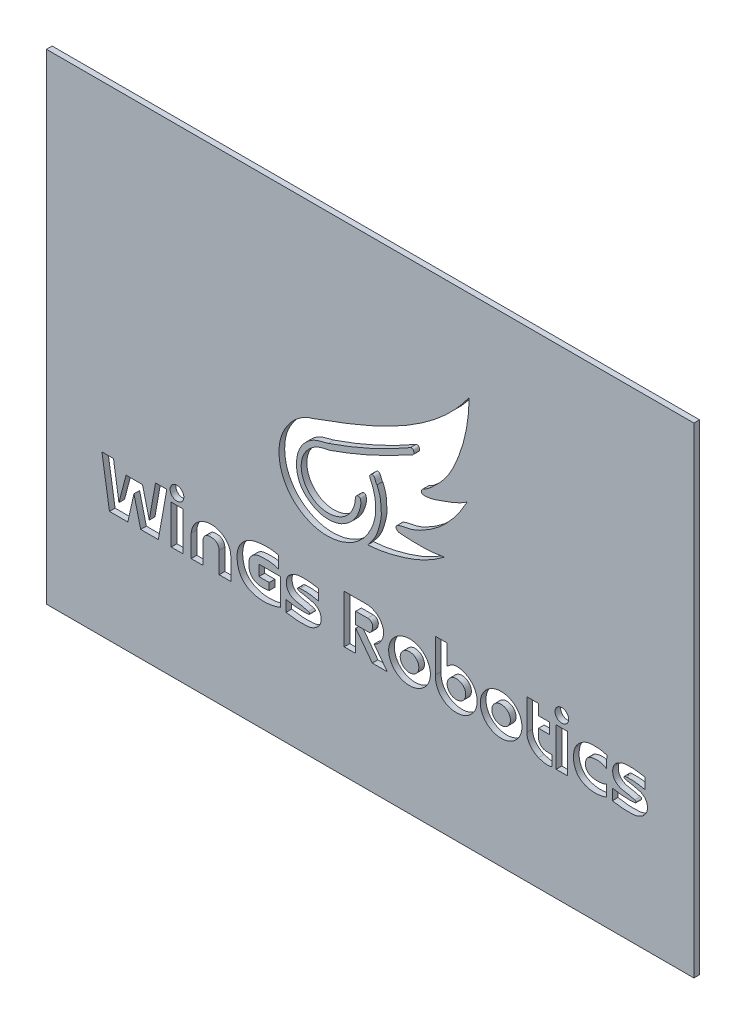
SolidWorks part; units mm, degrees
ref_plane "前视基准面" through (0, 0, 0) normal (0, 0, 1) x (1, 0, 0)
ref_plane "上视基准面" through (0, 0, 0) normal (0, 1, 0) x (1, 0, 0)
ref_plane "右视基准面" through (0, 0, 0) normal (1, 0, 0) x (0, 0, -1)
other "Configuration Table"
sketch "Sketch1" plane through (0, 0, 0) normal (0, 0, 1) x (1, 0, 0)
  line L1 (0, 0) -> (114.5, 0)
  line L2 (0, 0) -> (0, 85)
  line L3 (0, 85) -> (114.5, 85)
  line L4 (114.5, 0) -> (114.5, 85)
  dimension "D1" = 114.5
  dimension "D2" = 85
extrude "Boss-Extrude1" add sketch "Sketch1" along normal blind 1
sketch "Sketch2" plane through (0, 0, 1) normal (0, 0, 1) x (1, 0, 0)
  line L0 (9.8027, 28.235) -> (11.8527, 28.235)
  line L1 (11.8527, 28.235) -> (12.8123, 21.9684)
  line L2 (12.8123, 21.9684) -> (14.0773, 26.8101)
  line L3 (14.0773, 26.8101) -> (16.9852, 26.8101)
  line L4 (16.9852, 26.8101) -> (18.1775, 21.9684)
  line L5 (18.1775, 21.9684) -> (19.2825, 28.235)
  line L6 (19.2825, 28.235) -> (21.2744, 28.235)
  line L7 (21.2744, 28.235) -> (19.7853, 19.7903)
  line L8 (19.7853, 19.7903) -> (16.6653, 19.7903)
  line L9 (16.6653, 19.7903) -> (15.4678, 24.6536)
  line L10 (15.4678, 24.6536) -> (14.3826, 19.7903)
  line L11 (14.3826, 19.7903) -> (11.1403, 19.7903)
  line L12 (11.1403, 19.7903) -> (9.8027, 28.235)
  line L13 (22.0595, 26.6647) -> (24.1096, 26.6647)
  line L14 (24.1096, 26.6647) -> (24.1096, 19.7903)
  line L15 (24.1096, 19.7903) -> (22.0595, 19.7903)
  line L16 (22.0595, 19.7903) -> (22.0595, 26.6647)
  line L17 (32.5933, 23.6986) -> (32.5933, 19.7903)
  line L18 (32.5933, 19.7903) -> (30.5505, 19.7903)
  line L19 (30.5505, 19.7903) -> (30.5505, 23.5343)
  line L20 (27.6427, 23.5343) -> (27.6427, 19.7903)
  line L21 (27.6427, 19.7903) -> (25.5972, 19.7903)
  line L22 (25.5972, 19.7903) -> (25.5972, 23.6986)
  line L23 (41.4245, 20.2317) -> (41.4245, 24.9256)
  line L24 (41.4245, 24.9256) -> (37.5759, 24.9256)
  line L25 (37.5759, 24.9256) -> (37.5759, 23.026)
  line L26 (37.5759, 23.026) -> (39.3929, 23.026)
  line L27 (39.3929, 23.026) -> (39.3929, 21.7872)
  line L28 (41.0585, 28.009) -> (41.0585, 25.9029)
  line L29 (42.3726, 19.9426) -> (42.3726, 21.9041)
  line L30 (48.1482, 26.4281) -> (48.1482, 24.5174)
  line L31 (57.9509, 22.8769) -> (60.2681, 19.7995)
  line L32 (60.2681, 19.7995) -> (57.6234, 19.7995)
  line L33 (57.6234, 19.7995) -> (54.6991, 23.6831)
  line L34 (54.6991, 23.6831) -> (54.6991, 19.7995)
  line L35 (54.6991, 19.7995) -> (52.65, 19.7995)
  line L36 (52.65, 19.7995) -> (52.65, 28.3165)
  line L37 (52.65, 28.3165) -> (56.9933, 28.3165)
  line L38 (56.8114, 26.2746) -> (54.6991, 26.2746)
  line L39 (54.6991, 26.2746) -> (54.6991, 24.2045)
  line L40 (54.6991, 24.2045) -> (56.8948, 24.2045)
  line L41 (68.7934, 29.486) -> (70.8757, 29.486)
  line L42 (70.8757, 29.486) -> (70.8757, 25.9572)
  line L43 (68.7934, 29.486) -> (68.8194, 23.6311)
  line L44 (84.9748, 28.3165) -> (87.0193, 28.3165)
  line L45 (87.0193, 28.3165) -> (87.0193, 26.4281)
  line L46 (87.0193, 26.4281) -> (88.9274, 26.4281)
  line L47 (88.9274, 26.4281) -> (88.9274, 24.5174)
  line L48 (88.9274, 24.5174) -> (87.0193, 24.5174)
  line L49 (87.0193, 24.5174) -> (87.0193, 22.8769)
  line L50 (84.9748, 28.3165) -> (84.9748, 22.8769)
  line L51 (89.3697, 19.7903) -> (89.3697, 21.6564)
  line L52 (90.1423, 26.5997) -> (92.1233, 26.5997)
  line L53 (92.1233, 26.5997) -> (92.1233, 19.7903)
  line L54 (92.1233, 19.7903) -> (90.1423, 19.7903)
  line L55 (90.1423, 19.7903) -> (90.1423, 26.5997)
  line L56 (100.0817, 19.9352) -> (100.0817, 21.8967)
  line L57 (105.8573, 26.4207) -> (105.8573, 24.51)
  circle A0 centre (23.0773, 28.5403) radius 1.2139
  circle A1 centre (91.149, 28.5403) radius 1.2042
  ellipse E0 centre (64.2087, 23.2238) end of major axis (62.5755, 23.026) minor radius 1.6135
  ellipse E1 centre (64.2087, 23.2238) end of major axis (60.5207, 23.2238) minor radius 3.5863
  ellipse E2 centre (72.5089, 23.2351) end of major axis (70.8757, 23.0374) minor radius 1.6135
  ellipse E3 centre (72.4814, 23.2061) end of major axis (68.7937, 23.2519) minor radius 3.5627 (68.8194, 23.6311) -> (72.4501, 26.7688) ccw
  ellipse E4 centre (80.4111, 23.2582) end of major axis (78.7779, 23.0604) minor radius 1.6135
  ellipse E5 centre (80.4111, 23.2582) end of major axis (76.723, 23.2582) minor radius 3.5863
  spline S0 degree 3 poles (47.1831, 52.0268) (57.216, 55.6604) (68.3491, 59.9142) (74.7524, 69.0372) knots 0 0 0 0 1 1 1 1
  spline S1 degree 3 poles (74.7524, 69.0372) (74.7365, 65.3659) (73.7278, 60.4257) (70.9663, 54.8142) (68.7581, 52.5438) (67.3008, 51.2594) (66.3857, 50.8892) (66.1919, 50.0322) (67.3405, 50.0519) (68.5807, 50.2825) (71.1429, 51.2424) (73.2135, 51.9772) (74.4343, 52.9034) knots 0 0 0 0 0.360634 0.500005 0.614902 0.674582 0.691796 0.711227 0.738156 0.775636 0.851126 1 1 1 1
  spline S2 degree 3 poles (74.4343, 52.9034) (73.5344, 51.2446) (71.9363, 48.8706) (69.1717, 46.2263) (66.8129, 44.6852) (64.459, 43.5637) (62.7709, 43.442) (61.8385, 43.0103) (61.7928, 42.333) (62.306, 42.118) (62.5755, 42.1345) knots 0 0 0 0 0.317486 0.47747 0.639062 0.792073 0.904921 0.928219 0.95201 1 1 1 1
  spline S3 degree 3 poles (62.5755, 42.1345) (63.3547, 42.0538) (64.7001, 41.9914) (66.7084, 41.981) (68.5463, 42.1026) (69.8092, 42.2942) (70.4107, 42.4227) knots 0 0 0 0 0.298501 0.513418 0.765548 1 1 1 1
  spline S4 degree 3 poles (70.4107, 42.4227) (69.0722, 41.3928) (66.6735, 39.9566) (63.1137, 38.6779) (60.0189, 37.8594) (57.9209, 37.5758) (56.8114, 37.504) knots 0 0 0 0 0.345509 0.567874 0.772357 1 1 1 1
  spline S5 degree 3 poles (56.8114, 37.504) (57.1501, 38.014) (57.9873, 38.9045) (58.6132, 40.423) (59.0127, 41.8409) (59.2903, 43.2209) (59.1608, 44.4082) (59.1125, 45.8858) (58.7734, 46.8278) (58.4542, 47.5164) knots 0 0 0 0 0.171911 0.337536 0.453261 0.586014 0.727877 0.785411 1 1 1 1
  spline S6 degree 3 poles (58.4542, 47.5164) (58.1552, 47.7663) (58.2426, 48.4056) (57.6344, 48.7258) (57.3395, 48.5611) (57.1481, 48.3317) (57.1918, 47.9689) (57.3731, 47.5948) (57.6463, 47.0478) (57.8358, 46.4382) (58.0549, 45.6679) (58.1832, 44.9046) (58.2458, 43.8518) (58.2148, 42.7406) (57.9317, 41.5832) (57.6308, 40.6253) (57.1596, 39.7594) (56.5162, 38.6016) (55.4247, 37.4363) (54.1168, 36.4637) (52.8944, 35.9233) (51.7724, 35.5143) (50.4508, 35.3174) (48.7837, 35.2372) (46.8987, 35.6969) (44.9241, 36.6174) (43.1617, 38.1067) (42.0038, 39.9015) (41.341, 41.702) (41.0315, 43.7959) (41.2416, 46.0312) (42.3532, 48.424) (44.0891, 50.6501) (46.0639, 51.7314) (47.1831, 52.0268) knots 0 0 0 0 0.025484 0.033383 0.040232 0.046589 0.052344 0.063459 0.074884 0.093534 0.10647 0.129018 0.145625 0.17776 0.203591 0.22594 0.245355 0.270053 0.315285 0.351906 0.379455 0.405318 0.432327 0.469429 0.51742 0.561659 0.615846 0.670887 0.704018 0.744828 0.813277 0.85164 0.92215 1 1 1 1
  spline S7 degree 3 poles (64.3499, 56.1614) (64.4693, 56.198) (64.7382, 56.2478) (64.9298, 55.9871) (65.0268, 55.728) (64.8911, 55.1487) (64.274, 55.0547) (64.0386, 54.8823) knots 0 0 0 0 0.180535 0.288784 0.393192 0.542414 1 1 1 1
  spline S8 degree 3 poles (64.0386, 54.8823) (59.572, 52.4062) (54.9001, 50.2948) (50.0745, 48.6121) knots 0 0 0 0 1 1 1 1
  spline S9 degree 2 poles (64.3499, 56.1614) (57.4385, 52.1577) (49.8143, 49.5487) knots 0 0 0 1 1 1
  spline S10 degree 3 poles (49.8143, 49.5487) (49.1643, 49.3784) (48.2124, 49.1961) (46.3723, 48.3773) (44.2192, 46.161) (43.9774, 42.6043) (45.2254, 40.0525) (46.5951, 38.9146) (48.299, 37.9908) (50.179, 37.8379) (52.0127, 38.232) (53.3955, 39.1002) (54.5017, 40.1892) (55.1879, 41.4828) (55.5621, 42.6798) (55.6315, 43.5768) (55.4539, 44.1289) (55.208, 44.1161) knots 0 0 0 0 0.074167 0.1054 0.220595 0.394008 0.454413 0.527731 0.585289 0.665338 0.728528 0.788515 0.842168 0.897128 0.948286 0.97672 1 1 1 1
  spline S11 degree 3 poles (55.208, 44.1161) (55.0226, 44.1791) (54.667, 43.959) (54.6094, 43.4642) (54.5978, 42.8636) (54.3423, 42.0093) (53.7764, 40.7342) (52.3297, 39.3376) (50.1524, 38.7214) (47.7052, 39.1332) (45.9303, 40.6216) (44.9775, 42.794) (45.0428, 45.5373) (47.1244, 48.0082) (49.206, 48.4687) (50.0745, 48.6121) knots 0 0 0 0 0.023493 0.044042 0.061062 0.101136 0.156797 0.23921 0.350066 0.433771 0.549578 0.629423 0.732521 0.886291 1 1 1 1
  spline S12 degree 3 poles (25.5972, 23.6986) (25.655, 24.3658) (26.0941, 25.5117) (27.5424, 26.5737) (30.2768, 27.2067) (32.5736, 25.5619) (32.5933, 23.6986) knots 0 0 0 0 0.198571 0.34064 0.5135 1 1 1 1
  spline S13 degree 3 poles (30.5505, 23.5343) (30.5434, 23.9759) (30.1068, 24.7165) (29.076, 24.8585) (28.0074, 24.7723) (27.6729, 23.9331) (27.6427, 23.5343) knots 0 0 0 0 0.311205 0.495488 0.702071 1 1 1 1
  spline S14 degree 3 poles (41.0585, 28.009) (40.0534, 28.3395) (38.2528, 28.3483) (35.58, 27.8618) (33.8071, 26.0118) (33.5909, 23.4895) (34.2599, 21.0828) (36.5954, 19.6795) (39.0686, 19.544) (40.7235, 19.9364) (41.4245, 20.2317) knots 0 0 0 0 0.156695 0.267521 0.399378 0.502862 0.637623 0.747872 0.886035 1 1 1 1
  spline S15 degree 3 poles (39.3929, 21.7872) (38.7093, 21.6487) (37.5769, 21.5423) (36.1025, 22.3452) (35.7049, 23.7435) (35.8131, 25.2008) (36.9698, 26.204) (38.2345, 26.2733) (39.6234, 26.3182) (40.5236, 26.0878) (41.0585, 25.9029) knots 0 0 0 0 0.181467 0.284135 0.402884 0.534993 0.639881 0.765013 0.852735 1 1 1 1
  spline S16 degree 2 poles (48.1482, 24.5174) (46.544, 24.9457) (44.8888, 24.8527) knots 0 0 0 1 1 1
  spline S17 degree 2 poles (44.8888, 24.8527) (44.6892, 24.8488) (44.5108, 24.7528) knots 0 0 0 1 1 1
  spline S18 degree 3 poles (44.5108, 24.7528) (44.4063, 24.7177) (44.3879, 24.4124) (44.7022, 24.3838) (44.8061, 24.3456) knots 0 0 0 0 0.400794 1 1 1 1
  spline S19 degree 3 poles (44.8061, 24.3456) (45.4236, 24.274) (46.288, 24.0648) (47.4629, 23.8067) (48.147, 23.319) (48.5456, 22.5902) (48.6196, 21.7633) (48.3197, 20.8064) (47.5722, 20.1396) (46.6088, 19.7108) (45.569, 19.6812) (44.1213, 19.6404) (43.0613, 19.8702) (42.3726, 19.9426) knots 0 0 0 0 0.150366 0.217158 0.290606 0.346071 0.414261 0.48693 0.581715 0.647373 0.740089 0.830727 1 1 1 1
  spline S20 degree 3 poles (42.3726, 21.9041) (42.8525, 21.8037) (43.5405, 21.6847) (44.4782, 21.597) (45.1945, 21.5883) (45.8688, 21.5828) (46.3005, 21.6313) (46.5297, 21.6877) (46.5567, 21.797) (46.5523, 21.9643) (46.379, 22.021) (46.3173, 22.049) knots 0 0 0 0 0.315552 0.449833 0.605449 0.778844 0.876435 0.89782 0.91722 0.942476 1 1 1 1
  spline S21 degree 3 poles (46.3173, 22.049) (45.8247, 22.2107) (44.9758, 22.4016) (43.6481, 22.557) (42.7017, 23.2519) (42.4205, 24.1635) (42.4311, 24.8543) (42.5725, 25.4907) (43.0041, 26.0044) (43.5079, 26.3588) (44.1094, 26.601) (44.7443, 26.7343) (45.4456, 26.7433) (46.2623, 26.7426) (47.164, 26.593) (47.8325, 26.5196) (48.1482, 26.4281) knots 0 0 0 0 0.129354 0.21684 0.332807 0.395282 0.447956 0.504879 0.55359 0.611568 0.6573 0.714661 0.772387 0.8321 0.918346 1 1 1 1
  spline S22 degree 3 poles (56.9933, 28.3165) (57.5079, 28.1999) (58.406, 27.8613) (59.3049, 26.8025) (59.7648, 25.5393) (59.3451, 23.9707) (58.5781, 23.1135) (57.9509, 22.8769) knots 0 0 0 0 0.216647 0.372499 0.551297 0.738033 1 1 1 1
  spline S23 degree 3 poles (56.8114, 26.2746) (57.1651, 26.312) (57.7627, 25.8573) (57.663, 24.8197) (57.3325, 24.1932) (56.8948, 24.2045) knots 0 0 0 0 0.345185 0.626261 1 1 1 1
  spline S24 degree 3 poles (70.8757, 25.9572) (71.1665, 26.2093) (71.6761, 26.5782) (72.2834, 26.7779) (72.5256, 26.7686) knots 0 0 0 0 0.616176 1 1 1 1
  spline S25 degree 3 poles (84.9748, 22.8769) (84.9049, 21.5816) (85.8804, 20.4707) (87.0193, 20.0095) knots 0 0 0 0 1 1 1 1
  spline S26 degree 3 poles (87.0193, 20.0095) (87.7648, 19.7661) (88.5925, 19.5177) (89.3697, 19.7903) knots 0 0 0 0 1 1 1 1
  spline S27 degree 3 poles (89.3697, 21.6564) (88.8864, 21.6815) (88.1032, 21.5524) (87.2817, 22.1652) (87.0872, 22.6179) (87.0193, 22.8769) knots 0 0 0 0 0.51466 0.724878 1 1 1 1
  spline S28 degree 1 poles (99.1074, 26.4281) (99.0451, 24.3456) knots 0 0 1 1
  spline S29 degree 1 poles (99.0451, 21.9684) (99.0762, 20.0095) knots 0 0 1 1
  spline S30 degree 3 poles (99.0451, 24.3456) (98.1408, 24.9177) (96.9334, 25.0104) (95.9622, 24.5174) knots 0 0 0 0 1 1 1 1
  spline S31 degree 3 poles (95.9622, 24.5174) (95.5905, 24.3596) (95.3714, 23.8067) (95.285, 23.0241) (95.4658, 22.3958) (95.9075, 21.9602) (96.4713, 21.7289) (97.5261, 21.5847) (98.4341, 21.6572) (99.0451, 21.9684) knots 0 0 0 0 0.178932 0.272004 0.383259 0.483726 0.563109 0.676721 1 1 1 1
  spline S32 degree 3 poles (99.1074, 26.4281) (98.7068, 26.5706) (98.0571, 26.739) (97.1441, 26.7697) (96.4259, 26.789) (95.6235, 26.6801) (94.7667, 26.291) (94.0187, 25.6423) (93.3941, 24.7521) (93.1988, 23.7089) (93.1885, 22.6621) (93.4504, 21.6401) (94.6922, 19.4323) (97.6705, 19.3697) (99.0762, 20.0095) knots 0 0 0 0 0.080032 0.124598 0.171299 0.214887 0.2755 0.344981 0.398822 0.476451 0.539473 0.594477 0.673245 1 1 1 1
  spline S33 degree 2 poles (105.8573, 24.51) (104.2531, 24.9383) (102.5979, 24.8453) knots 0 0 0 1 1 1
  spline S34 degree 2 poles (102.5979, 24.8453) (102.3983, 24.8414) (102.2199, 24.7454) knots 0 0 0 1 1 1
  spline S35 degree 3 poles (102.2199, 24.7454) (102.1154, 24.7103) (102.097, 24.405) (102.4113, 24.3764) (102.5152, 24.3382) knots 0 0 0 0 0.400794 1 1 1 1
  spline S36 degree 3 poles (102.5152, 24.3382) (103.1327, 24.2666) (103.9971, 24.0574) (105.172, 23.7993) (105.8561, 23.3116) (106.2547, 22.5828) (106.3287, 21.7559) (106.0288, 20.799) (105.2813, 20.1322) (104.3179, 19.7034) (103.2781, 19.6738) (101.8304, 19.633) (100.7704, 19.8627) (100.0817, 19.9352) knots 0 0 0 0 0.150366 0.217158 0.290606 0.346071 0.414261 0.48693 0.581715 0.647373 0.740089 0.830727 1 1 1 1
  spline S37 degree 3 poles (100.0817, 21.8967) (100.5616, 21.7963) (101.2496, 21.6773) (102.1873, 21.5896) (102.9036, 21.5809) (103.5779, 21.5754) (104.0096, 21.6239) (104.2387, 21.6803) (104.2658, 21.7896) (104.2614, 21.9568) (104.0881, 22.0136) (104.0264, 22.0416) knots 0 0 0 0 0.315552 0.449833 0.605449 0.778844 0.876435 0.89782 0.91722 0.942476 1 1 1 1
  spline S38 degree 3 poles (104.0264, 22.0416) (103.5338, 22.2033) (102.6849, 22.3942) (101.3572, 22.5496) (100.4108, 23.2445) (100.1296, 24.1561) (100.1402, 24.8468) (100.2816, 25.4833) (100.7132, 25.997) (101.217, 26.3514) (101.8185, 26.5936) (102.4534, 26.7269) (103.1547, 26.7359) (103.9714, 26.7352) (104.8731, 26.5856) (105.5416, 26.5122) (105.8573, 26.4207) knots 0 0 0 0 0.129354 0.21684 0.332807 0.395282 0.447956 0.504879 0.55359 0.611568 0.6573 0.714661 0.772387 0.8321 0.918346 1 1 1 1
extrude "Cut-Extrude1" cut sketch "Sketch2" against normal blind 11 contours S6 S5 S4 S3 S2 S1 S0 S11 S10 S9 S7 S8 | L12 L11 L10 L9 L8 L7 L6 L5 L4 L3 L2 L1 L0 | L16 L15 L14 L13 | A0 | S13 L19 L18 L17 S12 L22 L21 L20 | L27 S15 L28 S14 L23 L24 L25 L26 | S21 S20 L29 S19 S18 S17 S16 L30 | S22 L37 L36 L35 L34 L33 L32 L31 L38 S23 L40 L39 | E1 E0 | S24 L42 L41 L43 E3 E2 | E5 E4 | L51 S27 L49 L48 L47 L46 L45 L44 L50 S25 S26 | L55 L54 L53 L52 | A1 | S28 S32 S29 S31 S30 | S38 S37 L56 S36 S35 S34 S33 L57
